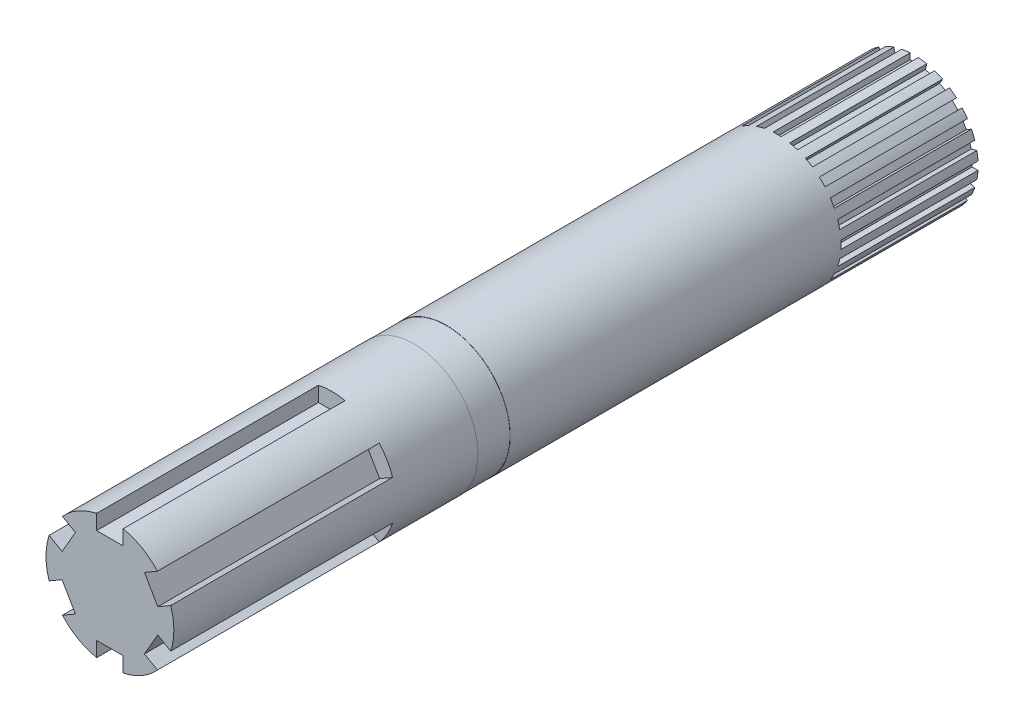
SolidWorks part; units mm, degrees
ref_plane "Front Plane" through (0, 0, 0) normal (0, 0, 1) x (1, 0, 0)
ref_plane "Top Plane" through (0, 0, 0) normal (0, 1, 0) x (1, 0, 0)
ref_plane "Right Plane" through (0, 0, 0) normal (1, 0, 0) x (0, 0, -1)
sketch "Sketch1" plane through (0, 0, 0) normal (0, 0, 1) x (1, 0, 0)
  circle A0 centre (0, 0) radius 7.925
extrude "Boss-Extrude1" add sketch "Sketch1" along normal blind 58
sketch "Sketch2" plane through (0, 0, 58) normal (0, 0, 1) x (1, 0, 0)
  circle A0 centre (0, 0) radius 7.9
extrude "Boss-Extrude2" add sketch "Sketch2" along normal blind 4
sketch "Sketch3" plane through (0, 0, 62) normal (0, 0, 1) x (1, 0, 0)
  circle A0 centre (0, 0) radius 7.925
extrude "Boss-Extrude3" add sketch "Sketch3" along normal blind 37.7
ref_plane "Plane2" through (0, 7.925, 0) normal (0, 1, 0) x (1, 0, 0)
sketch "Sketch4" plane through (0, 7.925, 0) normal (0, 1, 0) x (1, 0, 0)
  line L0 (-7.925, -99.7) -> (7.925, -99.7) construction
  line L1 (-1.651, -99.7) -> (1.651, -99.7)
  line L2 (-1.651, -99.7) -> (-1.651, -72.2)
  line L3 (-1.651, -72.2) -> (1.651, -72.2)
  line L4 (1.651, -99.7) -> (1.651, -72.2)
  line L5 (0, -8.7175) -> (0, 8.7175) construction
  dimension "D1" = 27.5
  dimension "D2" = 3.302
  dimension "D3" = 1.651
extrude "Cut-Extrude1" cut sketch "Sketch4" against normal blind 2.032 contours L2 L3 L4 L1
pattern_circular "CirPattern1" count 6 over 360 about axis through (0, 0, 0) along (0, 0, 1) of "Cut-Extrude1"
sketch "Sketch10" plane through (0, 7.925, 0) normal (0, 1, 0) x (1, 0, 0)
  line L1 (-0.5, -17) -> (0.5, -17)
  line L2 (-0.5, -17) -> (-0.5, 0)
  line L3 (-0.5, 0) -> (0.5, 0)
  line L4 (0.5, -17) -> (0.5, 0)
  line L5 (-0.5, -17) -> (0.5, 0) construction
  line L6 (-0.5, 0) -> (0.5, -17) construction
  line L9 (0, 0) -> (0, -17.7116) construction
  line L10 (0, 0.8468) -> (0, -16.8647) construction
  point P0 (0, -8.5)
  dimension "D1" = 17
  dimension "D2" = 1
extrude "Cut-Extrude2" cut sketch "Sketch10" against normal blind 0.75
pattern_circular "CirPattern2" count 24 over 360 about axis through (0, 0, 0) along (0, 0, 1) of "Cut-Extrude2"
equation "\"D2\"=0.065"
